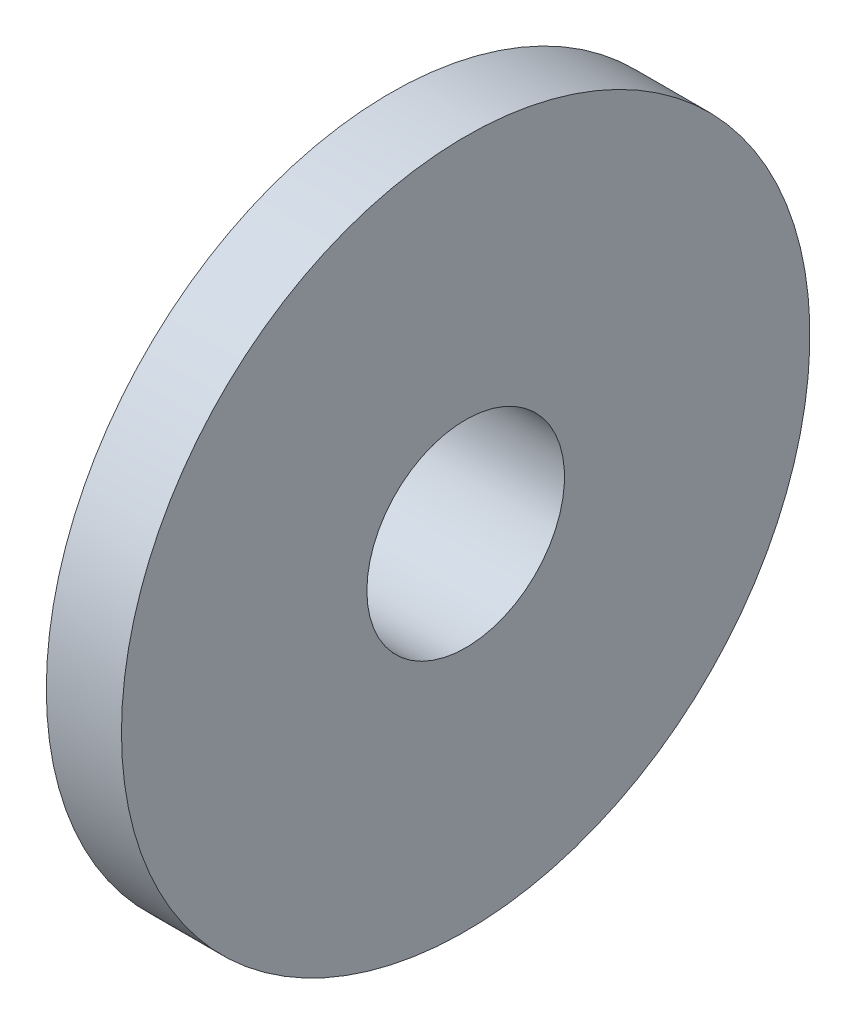
SolidWorks part; units mm, degrees
ref_plane "Front Plane" through (0, 0, 0) normal (0, 0, 1) x (1, 0, 0)
ref_plane "Top Plane" through (0, 0, 0) normal (0, 1, 0) x (1, 0, 0)
ref_plane "Right Plane" through (0, 0, 0) normal (1, 0, 0) x (0, 0, -1)
sketch "Sketch1" plane through (0, 0, 0) normal (0, 1, 0) x (1, 0, 0)
  line L0 (-8.7351, 16.2331) -> (-8.7351, 8.7479)
  line L1 (-8.7351, 8.7479) -> (0, 8.7479)
  line L2 (0, 8.7479) -> (0, 23.0069)
  line L3 (-8.7351, 16.2331) -> (-4.3675, 16.2331)
  line L4 (-4.3675, 16.2331) -> (-4.3675, 23.0069)
  line L5 (-4.3675, 23.0069) -> (0, 23.0069)
  line L6 (-12.0675, 3.0069) -> (3.181, 3.0069) construction
  dimension "D1" = 20
revolve "Revolve1" add sketch "Sketch1" angle 360 about L6
